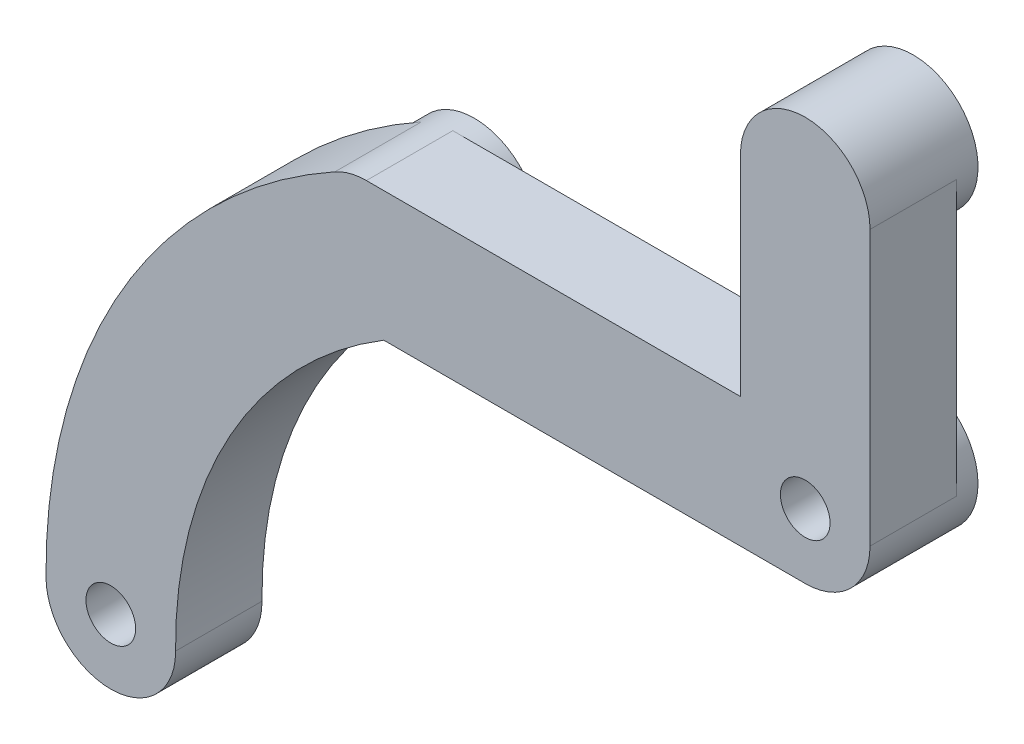
SolidWorks part; units mm, degrees
ref_plane "Ebene vorne" through (0, 0, 0) normal (0, 0, 1) x (1, 0, 0)
ref_plane "Ebene oben" through (0, 0, 0) normal (0, 1, 0) x (1, 0, 0)
ref_plane "Ebene rechts" through (0, 0, 0) normal (1, 0, 0) x (0, 0, -1)
sketch "Skizze1" plane through (0, 0, 0) normal (0, 0, 1) x (1, 0, 0)
  line L0 (-12.7, 6.477) -> (-12.7, -6.6734) construction
  line L2 (6.8591, 8.89) -> (-5.3058, 8.89) construction
  circle A0 centre (-2.54, 2.54) radius 3
  circle A1 centre (-2.54, 15.24) radius 3
  circle A2 centre (-22.86, 2.54) radius 3
  dimension "D1" = 6
extrude "Aufsatz-Linear austragen1" add sketch "Skizze1" along normal blind 5
sketch "Skizze2" plane through (0, 0, 5) normal (0, 0, 1) x (1, 0, 0)
  line L7 (-5.54, 15.24) -> (0.46, 15.24)
  line L8 (-5.54, 15.24) -> (-5.54, 2.54)
  line L9 (-5.54, 2.54) -> (0.46, 2.54)
  line L10 (0.46, 15.24) -> (0.46, 2.54)
  circle A3 centre (-2.54, 15.24) radius 3 construction
  circle A4 centre (-2.54, 2.54) radius 3 construction
  point P9 (-2.54, 15.24)
  point P10 (-2.54, 2.54)
extrude "Aufsatz-Linear austragen2" add sketch "Skizze2" against normal offset from surface (4 mm away) 1
sketch "Skizze3" plane through (0, 0, 5) normal (0, 0, 1) x (1, 0, 0)
  line L1 (-22.86, 5.54) -> (-2.54, 5.54)
  line L2 (-22.86, 5.54) -> (-22.86, -0.46)
  line L3 (-22.86, -0.46) -> (-2.54, -0.46)
  line L4 (-2.54, 5.54) -> (-2.54, -0.46)
  circle A0 centre (-22.86, 2.54) radius 3 construction
  arc A1 (-5.54, 2.54) -> (0.46, 2.54) centre (-2.54, 2.54) ccw construction
  point P10 (-22.86, 2.54)
extrude "Aufsatz-Linear austragen3" add sketch "Skizze3" against normal up to surface (4 mm away) up to face at (-2.54, 8.89, 1)
sketch "Skizze9" plane through (0, 0, 1) normal (0, 0, -1) x (-1, 0, 0)
  line L1 (21.4038, -0.0829) -> (24.3162, 5.1629)
  arc A0 (24.3162, 5.1629) -> (37.695, -17.8012) centre (11.6961, -17.5689) cw
  arc A1 (21.4038, -0.0829) -> (31.6953, -17.7476) centre (11.6961, -17.5689) cw
  circle A2 centre (22.86, 2.54) radius 3 construction
  arc A3 (37.695, -17.8012) -> (31.6953, -17.7476) centre (34.6951, -17.7744) cw
  circle A4 centre (34.6951, -17.7744) radius 3 construction
  dimension "D1" = 20
extrude "Aufsatz-Linear austragen6" add sketch "Skizze9" against normal up to surface (4 mm away) up to face at (-25.86, 2.54, 5)
sketch "Skizze10" plane through (0, 0, 1) normal (0, 0, -1) x (-1, 0, 0)
  circle A0 centre (34.6951, -17.7744) radius 3
  arc A1 (31.6953, -17.7476) -> (37.695, -17.8012) centre (34.6951, -17.7744) ccw construction
extrude "Aufsatz-Linear austragen7" add sketch "Skizze10" against normal up to surface (4 mm away)
sketch "Skizze11" plane through (0, 0, 0) normal (0, 0, -1) x (-1, 0, 0)
  line L0 (13.3589, 9.9443) -> (1.1455, -9.5972) construction
  circle A0 centre (2.54, 15.24) radius 1.7
  circle A6 centre (22.86, 2.54) radius 1.7
  circle A7 centre (22.86, 2.54) radius 3 construction
  dimension "D1" = 3.4
extrude "Schnitt-Linear austragen5" cut sketch "Skizze11" against normal blind 4
sketch "Skizze12" plane through (0, 0, 1) normal (0, 0, -1) x (-1, 0, 0)
  circle A0 centre (34.6951, -17.7744) radius 1.15
  arc A1 (31.6953, -17.7476) -> (37.695, -17.8012) centre (34.6951, -17.7744) ccw construction
  dimension "D1" = 2.3
extrude "Schnitt-Linear austragen6" cut sketch "Skizze12" against normal through all
sketch "Skizze14" plane through (0, 0, 0) normal (0, 0, -1) x (-1, 0, 0)
  circle A0 centre (2.54, 2.54) radius 1.15
  dimension "D1" = 2.3
extrude "Schnitt-Linear austragen8" cut sketch "Skizze14" against normal through all
sketch "Skizze15" plane through (0, 0, 0) normal (0, 0, -1) x (-1, 0, 0)
  circle A1 centre (2.54, 2.54) radius 1.15
  circle A2 centre (2.54, 2.54) radius 1.15 construction
  circle A3 centre (2.54, 2.54) radius 3
  arc A4 (2.54, -0.46) -> (-0.46, 2.54) centre (2.54, 2.54) ccw construction
extrude "Aufsatz-Linear austragen9" add sketch "Skizze15" against normal up to surface (8.13 mm away)
sketch "Skizze19" plane through (0, 0, 5) normal (0, 0, 1) x (1, 0, 0)
  line L1 (-46.372, 25.0483) -> (6.025, 25.0483)
  line L2 (-46.372, 25.0483) -> (-46.372, -26.8405)
  line L3 (-46.372, -26.8405) -> (6.025, -26.8405)
  line L4 (6.025, 25.0483) -> (6.025, -26.8405)
  arc A0 (-22.054, -0.46) -> (-31.6953, -17.7476) centre (-11.6961, -17.5689) ccw construction
extrude "Schnitt-Linear austragen12" cut sketch "Skizze19" along normal through all
equation "\"M2EinschmelzGewindeDurchmesser\"=3.4"
equation "\"M2EinschmelzGewindeTiefe\"= 4.0"
equation "\"M3EinschmelzGewindeDurchmesser\"= 4.2"
equation "\"M3EinschmelzGewindeTief\"= 5.7"
equation "\"M2SchraubeLoch\"=2.3"
equation "\"offSetVonGummiReifen\"= 3.0"
equation "\"D1@Skizze11\"=\"M2EinschmelzGewindeDurchmesser\""
equation "\"D1@Schnitt-Linear austragen5\"=\"M2EinschmelzGewindeTiefe\""
equation "\"D1@Skizze12\"=\"M2SchraubeLoch\""
equation "\"D1@Skizze14\"=\"M2SchraubeLoch\""
